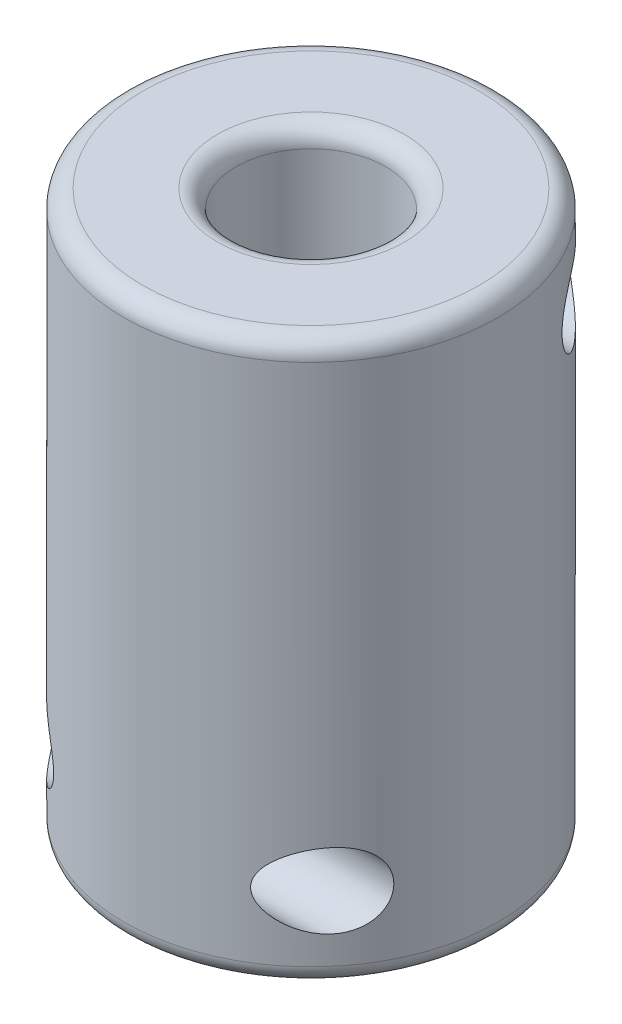
SolidWorks part; units mm, degrees
ref_plane "Front Plane" through (0, 0, 0) normal (0, 0, 1) x (1, 0, 0)
ref_plane "Top Plane" through (0, 0, 0) normal (0, 1, 0) x (1, 0, 0)
ref_plane "Right Plane" through (0, 0, 0) normal (1, 0, 0) x (0, 0, -1)
sketch "Sketch1" plane through (0, 0, 0) normal (0, 1, 0) x (1, 0, 0)
  circle A0 centre (0, 0) radius 4
  circle A1 centre (0, 0) radius 10
  dimension "D1" = 20
  dimension "D2" = 8
extrude "Boss-Extrude1" add sketch "Sketch1" along normal blind 30
sketch "Sketch2" plane through (0, 0, 0) normal (1, 0, 0) x (0, 0, -1)
  line L0 (10, 30) -> (-10, 30) construction
  line L1 (-10, 0) -> (10, 0) construction
  circle A0 centre (6.5, 25.5) radius 2
  circle A1 centre (-6.5, 4.5) radius 2
  dimension "D1" = 4
  dimension "D2" = 4.5
  dimension "D3" = 4.5
  dimension "D4" = 6.5
  dimension "D5" = 6.5
extrude "Cut-Extrude1" cut sketch "Sketch2" against normal through all both and the other way through all
fillet "Fillet1" radius 1 4 edges at (0, 0, 4) (0, 0, 10) (0, 30, 4) (0, 30, 10)
